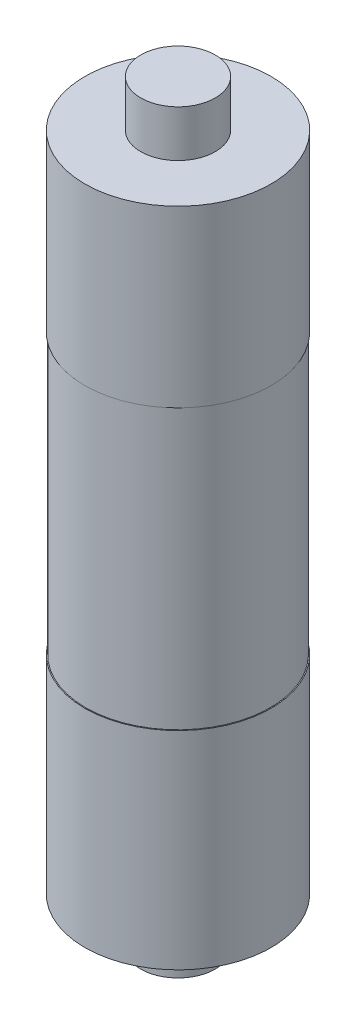
SolidWorks part; units mm, degrees
ref_plane "Alzado" through (0, 0, 0) normal (0, 0, 1) x (1, 0, 0)
ref_plane "Planta" through (0, 0, 0) normal (0, 1, 0) x (1, 0, 0)
ref_plane "Vista lateral" through (0, 0, 0) normal (1, 0, 0) x (0, 0, -1)
sketch "Croquis1" plane through (0, 0, 0) normal (0, 1, 0) x (1, 0, 0)
  circle A0 centre (0, 0) radius 10
  dimension "D1" = 20
extrude "Saliente-Extruir1" add sketch "Croquis1" along normal blind 71
sketch "Croquis2" plane through (0, 71, 0) normal (0, 1, 0) x (1, 0, 0)
  circle A0 centre (0, 0) radius 5
  dimension "D1" = 10
extrude "Cortar-Extruir1" [suppressed] cut sketch "Croquis2" against normal through all
sketch "Croquis3" plane through (0, 0, 0) normal (1, 0, 0) x (0, 0, -1)
  line L0 (10, 0) -> (10, 71) construction
  line L1 (10, 22.25) -> (9.9, 22.25)
  line L2 (10, 22.25) -> (10, 52.25)
  line L3 (10, 52.25) -> (9.9, 52.25)
  line L4 (9.9, 22.25) -> (9.9, 52.25)
  line L5 (10, 71) -> (-10, 71) construction
  line L6 (0, 71) -> (0, 19.3362) construction
  point P6 (9.95, 52.25)
  dimension "D1" = 30
  dimension "D2" = 18.75
  dimension "D3" = 0.1
revolve "Cortar-Revolución1" cut sketch "Croquis3" angle 360 about L6
sketch "Croquis4" plane through (0, 0, 0) normal (0, -1, 0) x (-1, 0, 0)
  circle A0 centre (0, 0) radius 4
  dimension "D1" = 8
extrude "Saliente-Extruir2" add sketch "Croquis4" along normal blind 5
sketch "Croquis5" plane through (0, 71, 0) normal (0, 1, 0) x (1, 0, 0)
  circle A0 centre (0, 0) radius 4
  dimension "D1" = 8
extrude "Saliente-Extruir3" add sketch "Croquis5" along normal blind 5
